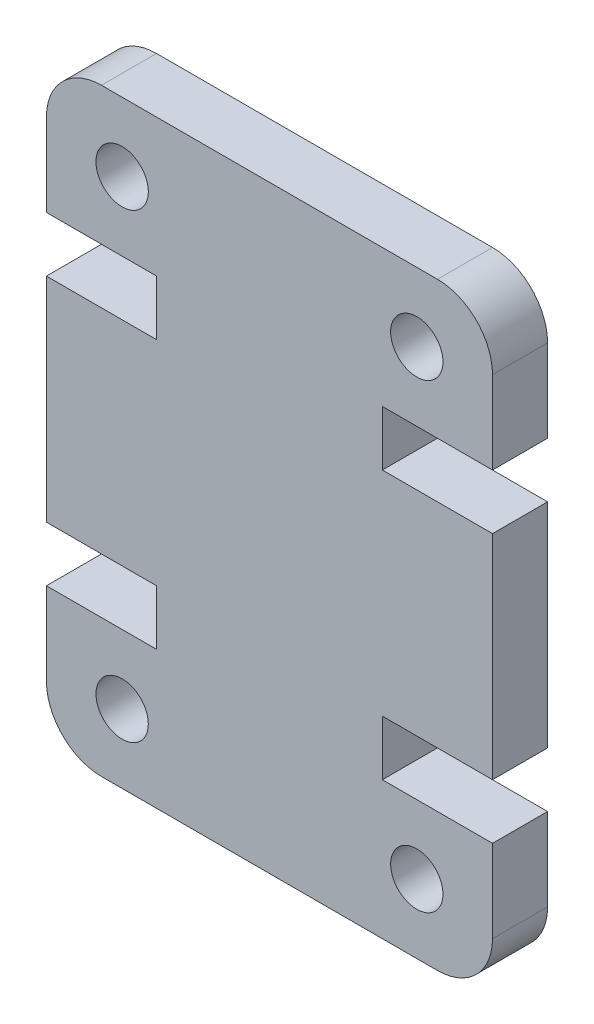
SolidWorks part; units mm, degrees
ref_plane "Front Plane" through (0, 0, 0) normal (0, 0, 1) x (1, 0, 0)
ref_plane "Top Plane" through (0, 0, 0) normal (0, 1, 0) x (1, 0, 0)
ref_plane "Right Plane" through (0, 0, 0) normal (1, 0, 0) x (0, 0, -1)
sketch "Sketch1" plane through (0, 0, 0) normal (0, 0, 1) x (1, 0, 0)
  line L0 (0, 14.74) -> (0, 7)
  line L1 (16.2, 2) -> (16.2, 5)
  line L2 (12.2, 5) -> (16.2, 5)
  line L3 (2, 0) -> (14.2, 0)
  line L4 (16.2, 7) -> (12.2, 7)
  line L5 (12.2, 7) -> (12.2, 5)
  line L6 (16.2, 14.74) -> (16.2, 7)
  line L7 (4, 7) -> (4, 5)
  line L8 (0, 19.74) -> (0, 16.74)
  line L9 (4, 16.74) -> (0, 16.74)
  line L10 (0, 7) -> (4, 7)
  line L11 (0, 14.74) -> (4, 14.74)
  line L12 (4, 5) -> (0, 5)
  line L13 (4, 14.74) -> (4, 16.74)
  line L14 (12.2, 14.74) -> (12.2, 16.74)
  line L15 (16.2, 14.74) -> (12.2, 14.74)
  line L16 (0, 2) -> (0, 5)
  line L17 (2, 21.74) -> (14.2, 21.74)
  line L18 (12.2, 16.74) -> (16.2, 16.74)
  line L19 (16.2, 19.74) -> (16.2, 16.74)
  line L20 (8.1, 21.74) -> (8.1, 0) construction
  line L21 (0, 10.87) -> (16.2, 10.87) construction
  circle A0 centre (13.45, 2.5) radius 0.95
  arc A1 (16.2, 2) -> (14.2, 0) centre (14.2, 2) cw
  circle A2 centre (2.75, 19.24) radius 0.95
  arc A3 (0, 2) -> (2, 0) centre (2, 2) ccw
  arc A4 (0, 19.74) -> (2, 21.74) centre (2, 19.74) cw
  circle A5 centre (2.75, 2.5) radius 0.95
  arc A6 (16.2, 19.74) -> (14.2, 21.74) centre (14.2, 19.74) ccw
  circle A7 centre (13.45, 19.24) radius 0.95
  point P15 (8.1, 10.87)
  dimension "D1" = 1.9
  dimension "D2" = 2
  dimension "D3" = 2.75
  dimension "D4" = 8.1
  dimension "D5" = 2.5
  dimension "D6" = 5
  dimension "D8" = 10.87
extrude "Boss-Extrude1" add sketch "Sketch1" along normal blind 4
sketch "Sketch2" plane through (0, 0, 0) normal (0, 0, -1) x (-1, 0, 0)
  line L0 (0, 0) -> (-16.2, 0)
  line L1 (-16.2, 0) -> (-16.2, 21.74)
  line L2 (-16.2, 21.74) -> (0, 21.74)
  line L3 (0, 21.74) -> (0, 0)
extrude "Cut-Extrude1" cut sketch "Sketch2" against normal blind 2
equation "\"D4@Sketch1\"= \"fingerWidth@parametersSketch@prostheticParameters.SLDPRT\" / 2'PIP width"
equation "\"D8@Sketch1\"= ( \"HL@parametersSketch@prostheticParameters.SLDPRT\" * 0.204 - 4 - 12 ) / 2 'PIP length - Sil. Sht MIP - Sil.Sht PIP"
equation "\"D1@Sketch1\"= 1.5 + \"tol1@parametersSketch@prostheticParameters.SLDPRT\""
